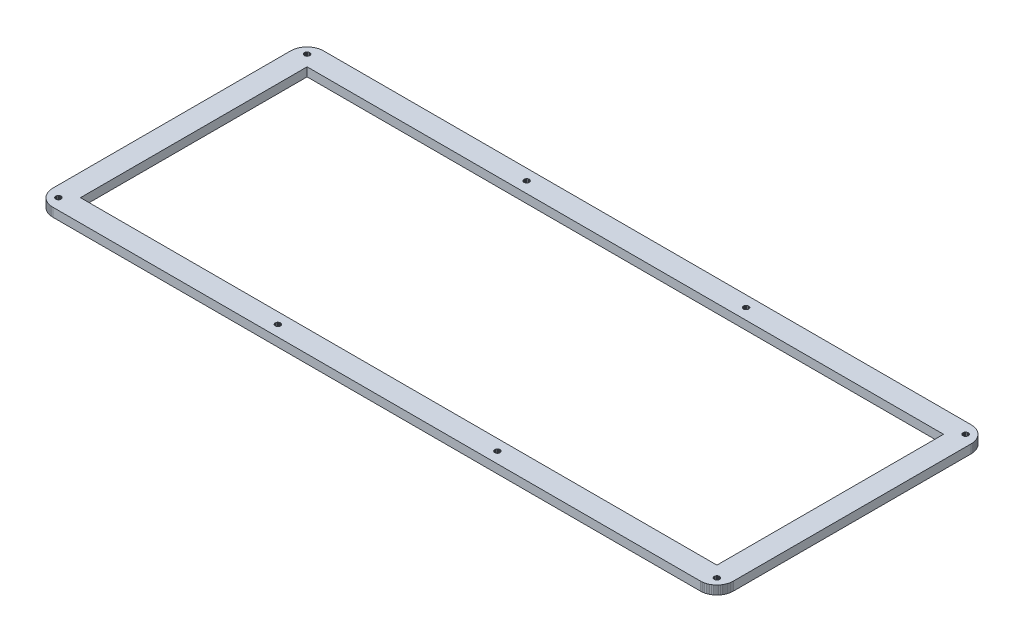
SolidWorks part; units mm, degrees
material "Copper"
ref_plane "Front Plane" through (0, 0, 0) normal (0, 0, 1) x (1, 0, 0)
ref_plane "Top Plane" through (0, 0, 0) normal (0, 1, 0) x (1, 0, 0)
ref_plane "Right Plane" through (0, 0, 0) normal (1, 0, 0) x (0, 0, -1)
sketch "Sketch1" plane through (0, 0, 0) normal (0, 1, 0) x (1, 0, 0)
  line L0 (362.807, 147.967) -> (363.513, 147.941)
  line L1 (363.513, 147.941) -> (364.215, 147.857)
  line L2 (364.215, 147.857) -> (364.91, 147.719)
  line L3 (364.91, 147.719) -> (365.591, 147.527)
  line L4 (365.591, 147.527) -> (366.254, 147.282)
  line L5 (366.254, 147.282) -> (366.896, 146.987)
  line L6 (366.896, 146.987) -> (367.51, 146.641)
  line L7 (367.51, 146.641) -> (368.099, 146.25)
  line L8 (368.099, 146.25) -> (368.653, 145.812)
  line L9 (368.653, 145.812) -> (369.171, 145.331)
  line L10 (369.171, 145.331) -> (369.651, 144.812)
  line L11 (369.651, 144.812) -> (370.089, 144.259)
  line L12 (370.089, 144.259) -> (370.48, 143.67)
  line L13 (370.48, 143.67) -> (370.826, 143.053)
  line L14 (370.826, 143.053) -> (371.122, 142.412)
  line L15 (371.122, 142.412) -> (371.369, 141.749)
  line L16 (371.369, 141.749) -> (371.56, 141.07)
  line L17 (371.56, 141.07) -> (371.697, 140.375)
  line L18 (371.697, 140.375) -> (371.778, 139.674)
  line L19 (371.778, 139.674) -> (371.807, 138.967)
  line L20 (371.807, 138.967) -> (371.807, 9.0909)
  line L21 (371.807, 9.0909) -> (371.778, 8.3854)
  line L22 (371.778, 8.3854) -> (371.697, 7.684)
  line L23 (371.697, 7.684) -> (371.56, 6.9908)
  line L24 (371.56, 6.9908) -> (371.369, 6.31)
  line L25 (371.369, 6.31) -> (371.122, 5.6472)
  line L26 (371.122, 5.6472) -> (370.826, 5.0064)
  line L27 (370.826, 5.0064) -> (370.48, 4.3891)
  line L28 (370.48, 4.3891) -> (370.089, 3.8006)
  line L29 (370.089, 3.8006) -> (369.651, 3.2467)
  line L30 (369.651, 3.2467) -> (369.171, 2.7285)
  line L31 (369.171, 2.7285) -> (368.653, 2.2476)
  line L32 (368.653, 2.2476) -> (368.099, 1.8107)
  line L33 (368.099, 1.8107) -> (367.51, 1.418)
  line L34 (367.51, 1.418) -> (366.896, 1.0721)
  line L35 (366.896, 1.0721) -> (366.254, 0.7772)
  line L36 (366.254, 0.7772) -> (365.591, 0.5319)
  line L37 (365.591, 0.5319) -> (364.91, 0.3404)
  line L38 (364.91, 0.3404) -> (364.215, 0.2026)
  line L39 (364.215, 0.2026) -> (363.513, 0.1185)
  line L40 (363.513, 0.1185) -> (362.807, 0.091)
  line L41 (362.807, 0.091) -> (9.0951, 0.091)
  line L42 (9.0951, 0.091) -> (8.3881, 0.1185)
  line L43 (8.3881, 0.1185) -> (7.6867, 0.2026)
  line L44 (7.6867, 0.2026) -> (6.9922, 0.3404)
  line L45 (6.9922, 0.3404) -> (6.3128, 0.5319)
  line L46 (6.3128, 0.5319) -> (5.6499, 0.7772)
  line L47 (5.6499, 0.7772) -> (5.0092, 1.0721)
  line L48 (5.0092, 1.0721) -> (4.3918, 1.418)
  line L49 (4.3918, 1.418) -> (3.8034, 1.8107)
  line L50 (3.8034, 1.8107) -> (3.2494, 2.2476)
  line L51 (3.2494, 2.2476) -> (2.7313, 2.7285)
  line L52 (2.7313, 2.7285) -> (2.2503, 3.2467)
  line L53 (2.2503, 3.2467) -> (1.8121, 3.8006)
  line L54 (1.8121, 3.8006) -> (1.4208, 4.3891)
  line L55 (1.4208, 4.3891) -> (1.0749, 5.0064)
  line L56 (1.0749, 5.0064) -> (0.78, 5.6472)
  line L57 (0.78, 5.6472) -> (0.5347, 6.31)
  line L58 (0.5347, 6.31) -> (0.3431, 6.9908)
  line L59 (0.3431, 6.9908) -> (0.2053, 7.684)
  line L60 (0.2053, 7.684) -> (0.1213, 8.3854)
  line L61 (0.1213, 8.3854) -> (0.0937, 9.0923)
  line L62 (0.0937, 9.0923) -> (0.0951, 138.967)
  line L63 (0.0951, 138.967) -> (0.1213, 139.674)
  line L64 (0.1213, 139.674) -> (0.2053, 140.375)
  line L65 (0.2053, 140.375) -> (0.3431, 141.07)
  line L66 (0.3431, 141.07) -> (0.5347, 141.749)
  line L67 (0.5347, 141.749) -> (0.78, 142.412)
  line L68 (0.78, 142.412) -> (1.0749, 143.053)
  line L69 (1.0749, 143.053) -> (1.4208, 143.67)
  line L70 (1.4208, 143.67) -> (1.8121, 144.259)
  line L71 (1.8121, 144.259) -> (2.2503, 144.812)
  line L72 (2.2503, 144.812) -> (2.7313, 145.331)
  line L73 (2.7313, 145.331) -> (3.2494, 145.812)
  line L74 (3.2494, 145.812) -> (3.8034, 146.25)
  line L75 (3.8034, 146.25) -> (4.3918, 146.641)
  line L76 (4.3918, 146.641) -> (5.0092, 146.987)
  line L77 (5.0092, 146.987) -> (5.6499, 147.282)
  line L78 (5.6499, 147.282) -> (6.3128, 147.527)
  line L79 (6.3128, 147.527) -> (6.9922, 147.719)
  line L80 (6.9922, 147.719) -> (7.6867, 147.857)
  line L81 (7.6867, 147.857) -> (8.3881, 147.941)
  line L82 (8.3881, 147.941) -> (9.0951, 147.968)
  line L83 (9.0951, 147.968) -> (362.807, 147.967)
  line L84 (365.326, 7.5186) -> (364.917, 7.3119)
  line L85 (364.917, 7.3119) -> (364.589, 6.9825)
  line L86 (364.589, 6.9825) -> (364.381, 6.5719)
  line L87 (364.381, 6.5719) -> (364.307, 6.1157)
  line L88 (364.307, 6.1157) -> (364.381, 5.661)
  line L89 (364.381, 5.661) -> (364.589, 5.2503)
  line L90 (364.589, 5.2503) -> (364.917, 4.9237)
  line L91 (364.917, 4.9237) -> (365.326, 4.7143)
  line L92 (365.326, 4.7143) -> (365.781, 4.6413)
  line L93 (365.781, 4.6413) -> (366.24, 4.7143)
  line L94 (366.24, 4.7143) -> (366.649, 4.9237)
  line L95 (366.649, 4.9237) -> (366.977, 5.2503)
  line L96 (366.977, 5.2503) -> (367.185, 5.661)
  line L97 (367.185, 5.661) -> (367.259, 6.1157)
  line L98 (367.259, 6.1157) -> (367.185, 6.5719)
  line L99 (367.185, 6.5719) -> (366.977, 6.9825)
  line L100 (366.977, 6.9825) -> (366.649, 7.3119)
  line L101 (366.649, 7.3119) -> (366.24, 7.5186)
  line L102 (366.24, 7.5186) -> (365.781, 7.5916)
  line L103 (365.781, 7.5916) -> (365.326, 7.5186)
  line L104 (245.438, 7.5186) -> (245.027, 7.3119)
  line L105 (245.027, 7.3119) -> (244.703, 6.9825)
  line L106 (244.703, 6.9825) -> (244.492, 6.5719)
  line L107 (244.492, 6.5719) -> (244.42, 6.1157)
  line L108 (244.42, 6.1157) -> (244.492, 5.661)
  line L109 (244.492, 5.661) -> (244.703, 5.2503)
  line L110 (244.703, 5.2503) -> (245.027, 4.9237)
  line L111 (245.027, 4.9237) -> (245.438, 4.7143)
  line L112 (245.438, 4.7143) -> (245.894, 4.6413)
  line L113 (245.894, 4.6413) -> (246.35, 4.7143)
  line L114 (246.35, 4.7143) -> (246.761, 4.9237)
  line L115 (246.761, 4.9237) -> (247.088, 5.2503)
  line L116 (247.088, 5.2503) -> (247.297, 5.661)
  line L117 (247.297, 5.661) -> (247.37, 6.1157)
  line L118 (247.37, 6.1157) -> (247.297, 6.5719)
  line L119 (247.297, 6.5719) -> (247.088, 6.9825)
  line L120 (247.088, 6.9825) -> (246.761, 7.3119)
  line L121 (246.761, 7.3119) -> (246.35, 7.5186)
  line L122 (246.35, 7.5186) -> (245.894, 7.5916)
  line L123 (245.894, 7.5916) -> (245.438, 7.5186)
  line L124 (125.552, 7.5186) -> (125.138, 7.3119)
  line L125 (125.138, 7.3119) -> (124.815, 6.9825)
  line L126 (124.815, 6.9825) -> (124.604, 6.5719)
  line L127 (124.604, 6.5719) -> (124.532, 6.1157)
  line L128 (124.532, 6.1157) -> (124.604, 5.661)
  line L129 (124.604, 5.661) -> (124.815, 5.2503)
  line L130 (124.815, 5.2503) -> (125.138, 4.9237)
  line L131 (125.138, 4.9237) -> (125.552, 4.7143)
  line L132 (125.552, 4.7143) -> (126.007, 4.6413)
  line L133 (126.007, 4.6413) -> (126.463, 4.7143)
  line L134 (126.463, 4.7143) -> (126.873, 4.9237)
  line L135 (126.873, 4.9237) -> (127.201, 5.2503)
  line L136 (127.201, 5.2503) -> (127.409, 5.661)
  line L137 (127.409, 5.661) -> (127.482, 6.1157)
  line L138 (127.482, 6.1157) -> (127.409, 6.5719)
  line L139 (127.409, 6.5719) -> (127.201, 6.9825)
  line L140 (127.201, 6.9825) -> (126.873, 7.3119)
  line L141 (126.873, 7.3119) -> (126.463, 7.5186)
  line L142 (126.463, 7.5186) -> (126.007, 7.5916)
  line L143 (126.007, 7.5916) -> (125.552, 7.5186)
  line L144 (5.6637, 7.5186) -> (5.2531, 7.3119)
  line L145 (5.2531, 7.3119) -> (4.9251, 6.9825)
  line L146 (4.9251, 6.9825) -> (4.717, 6.5719)
  line L147 (4.717, 6.5719) -> (4.644, 6.1157)
  line L148 (4.644, 6.1157) -> (4.717, 5.661)
  line L149 (4.717, 5.661) -> (4.9251, 5.2503)
  line L150 (4.9251, 5.2503) -> (5.2531, 4.9237)
  line L151 (5.2531, 4.9237) -> (5.6637, 4.7143)
  line L152 (5.6637, 4.7143) -> (6.1185, 4.6413)
  line L153 (6.1185, 4.6413) -> (6.5746, 4.7143)
  line L154 (6.5746, 4.7143) -> (6.9853, 4.9237)
  line L155 (6.9853, 4.9237) -> (7.3133, 5.2503)
  line L156 (7.3133, 5.2503) -> (7.5213, 5.661)
  line L157 (7.5213, 5.661) -> (7.5944, 6.1157)
  line L158 (7.5944, 6.1157) -> (7.5213, 6.5719)
  line L159 (7.5213, 6.5719) -> (7.3133, 6.9825)
  line L160 (7.3133, 6.9825) -> (6.9853, 7.3119)
  line L161 (6.9853, 7.3119) -> (6.5746, 7.5186)
  line L162 (6.5746, 7.5186) -> (6.1185, 7.5916)
  line L163 (6.1185, 7.5916) -> (5.6637, 7.5186)
  line L164 (12.1447, 135.919) -> (359.759, 135.919)
  line L165 (359.759, 135.919) -> (359.759, 12.1405)
  line L166 (359.759, 12.1405) -> (12.1447, 12.1405)
  line L167 (12.1447, 12.1405) -> (12.1447, 135.919)
  line L168 (125.552, 143.345) -> (125.138, 143.137)
  line L169 (125.138, 143.137) -> (124.815, 142.809)
  line L170 (124.815, 142.809) -> (124.604, 142.398)
  line L171 (124.604, 142.398) -> (124.532, 141.942)
  line L172 (124.532, 141.942) -> (124.604, 141.487)
  line L173 (124.604, 141.487) -> (124.815, 141.077)
  line L174 (124.815, 141.077) -> (125.138, 140.75)
  line L175 (125.138, 140.75) -> (125.552, 140.541)
  line L176 (125.552, 140.541) -> (126.007, 140.468)
  line L177 (126.007, 140.468) -> (126.463, 140.541)
  line L178 (126.463, 140.541) -> (126.873, 140.75)
  line L179 (126.873, 140.75) -> (127.201, 141.077)
  line L180 (127.201, 141.077) -> (127.409, 141.487)
  line L181 (127.409, 141.487) -> (127.482, 141.942)
  line L182 (127.482, 141.942) -> (127.409, 142.398)
  line L183 (127.409, 142.398) -> (127.201, 142.809)
  line L184 (127.201, 142.809) -> (126.873, 143.137)
  line L185 (126.873, 143.137) -> (126.463, 143.345)
  line L186 (126.463, 143.345) -> (126.007, 143.417)
  line L187 (126.007, 143.417) -> (125.552, 143.345)
  line L188 (245.438, 143.345) -> (245.027, 143.137)
  line L189 (245.027, 143.137) -> (244.703, 142.809)
  line L190 (244.703, 142.809) -> (244.492, 142.398)
  line L191 (244.492, 142.398) -> (244.42, 141.942)
  line L192 (244.42, 141.942) -> (244.492, 141.487)
  line L193 (244.492, 141.487) -> (244.703, 141.077)
  line L194 (244.703, 141.077) -> (245.027, 140.75)
  line L195 (245.027, 140.75) -> (245.438, 140.541)
  line L196 (245.438, 140.541) -> (245.894, 140.468)
  line L197 (245.894, 140.468) -> (246.35, 140.541)
  line L198 (246.35, 140.541) -> (246.761, 140.75)
  line L199 (246.761, 140.75) -> (247.088, 141.077)
  line L200 (247.088, 141.077) -> (247.297, 141.487)
  line L201 (247.297, 141.487) -> (247.37, 141.942)
  line L202 (247.37, 141.942) -> (247.297, 142.398)
  line L203 (247.297, 142.398) -> (247.088, 142.809)
  line L204 (247.088, 142.809) -> (246.761, 143.137)
  line L205 (246.761, 143.137) -> (246.35, 143.345)
  line L206 (246.35, 143.345) -> (245.894, 143.417)
  line L207 (245.894, 143.417) -> (245.438, 143.345)
  line L208 (365.326, 143.345) -> (364.917, 143.137)
  line L209 (364.917, 143.137) -> (364.589, 142.809)
  line L210 (364.589, 142.809) -> (364.381, 142.398)
  line L211 (364.381, 142.398) -> (364.307, 141.942)
  line L212 (364.307, 141.942) -> (364.381, 141.487)
  line L213 (364.381, 141.487) -> (364.589, 141.077)
  line L214 (364.589, 141.077) -> (364.917, 140.75)
  line L215 (364.917, 140.75) -> (365.326, 140.541)
  line L216 (365.326, 140.541) -> (365.781, 140.468)
  line L217 (365.781, 140.468) -> (366.24, 140.541)
  line L218 (366.24, 140.541) -> (366.649, 140.75)
  line L219 (366.649, 140.75) -> (366.977, 141.077)
  line L220 (366.977, 141.077) -> (367.185, 141.487)
  line L221 (367.185, 141.487) -> (367.259, 141.942)
  line L222 (367.259, 141.942) -> (367.185, 142.398)
  line L223 (367.185, 142.398) -> (366.977, 142.809)
  line L224 (366.977, 142.809) -> (366.649, 143.137)
  line L225 (366.649, 143.137) -> (366.24, 143.345)
  line L226 (366.24, 143.345) -> (365.781, 143.417)
  line L227 (365.781, 143.417) -> (365.326, 143.345)
  line L228 (5.6637, 143.345) -> (5.2531, 143.137)
  line L229 (5.2531, 143.137) -> (4.9251, 142.809)
  line L230 (4.9251, 142.809) -> (4.717, 142.398)
  line L231 (4.717, 142.398) -> (4.644, 141.942)
  line L232 (4.644, 141.942) -> (4.717, 141.487)
  line L233 (4.717, 141.487) -> (4.9251, 141.077)
  line L234 (4.9251, 141.077) -> (5.2531, 140.75)
  line L235 (5.2531, 140.75) -> (5.6637, 140.541)
  line L236 (5.6637, 140.541) -> (6.1185, 140.468)
  line L237 (6.1185, 140.468) -> (6.5746, 140.541)
  line L238 (6.5746, 140.541) -> (6.9853, 140.75)
  line L239 (6.9853, 140.75) -> (7.3133, 141.077)
  line L240 (7.3133, 141.077) -> (7.5213, 141.487)
  line L241 (7.5213, 141.487) -> (7.5944, 141.942)
  line L242 (7.5944, 141.942) -> (7.5213, 142.398)
  line L243 (7.5213, 142.398) -> (7.3133, 142.809)
  line L244 (7.3133, 142.809) -> (6.9853, 143.137)
  line L245 (6.9853, 143.137) -> (6.5746, 143.345)
  line L246 (6.5746, 143.345) -> (6.1185, 143.417)
  line L247 (6.1185, 143.417) -> (5.6637, 143.345)
extrude "Boss-Extrude1" add sketch "Sketch1" along normal blind 4.7625
